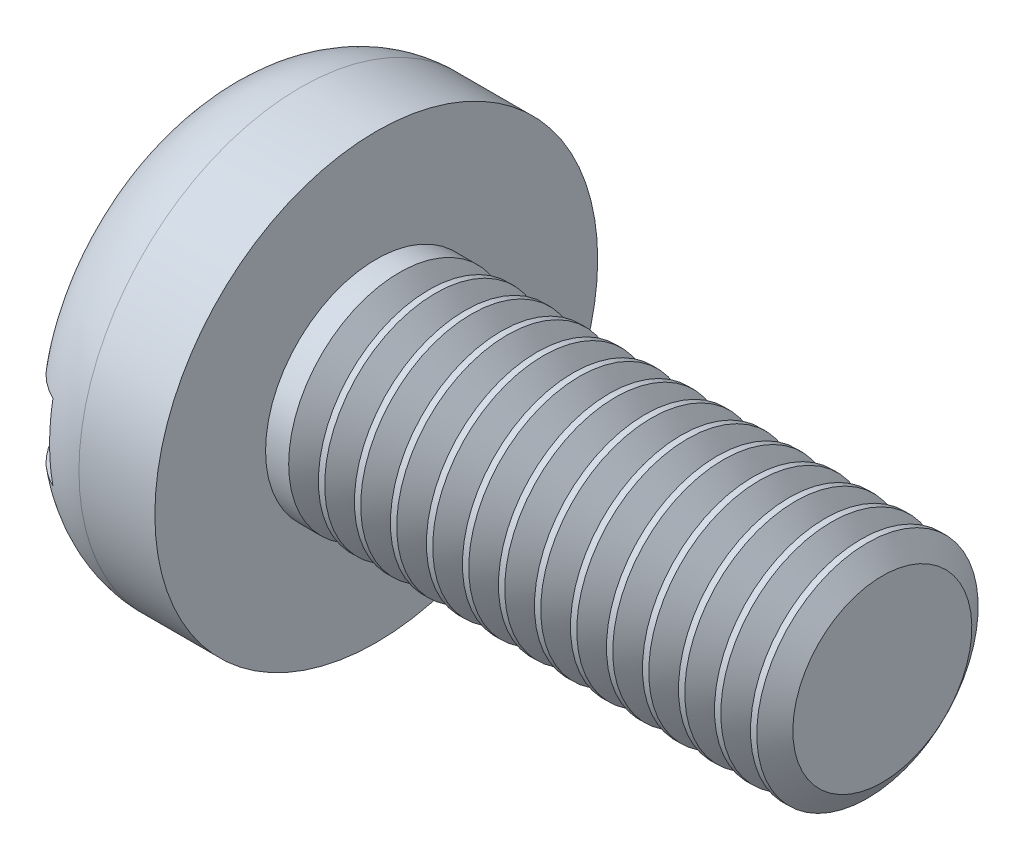
SolidWorks part; units mm, degrees
ref_plane "Plane1" through (0, 0, 0) normal (0, 0, 1) x (1, 0, 0)
ref_plane "Plane2" through (0, 0, 0) normal (0, 1, 0) x (1, 0, 0)
ref_plane "Plane3" through (0, 0, 0) normal (1, 0, 0) x (0, 0, -1)
sketch "BodySke" plane through (0, 0, 0) normal (0, 0, 1) x (1, 0, 0)
  line L0 (2.6, 1.75) -> (2.6, 3.5)
  line L1 (0, 0) -> (0, 2.1)
  line L2 (-25.4, 0) -> (127, 0) construction
  line L3 (10.6, 0) -> (0, 0)
  line L4 (2.6, 1.75) -> (10.6, 1.75)
  line L5 (10.6, 1.75) -> (10.6, 0)
  line L6 (1.4, 3.5) -> (2.6, 3.5)
  line L7 (2.6, -1.75) -> (10.6, -1.75) construction
  line L8 (0, -3.5) -> (2.6, -3.5) construction
  line L9 (3.2, 3.3375) -> (3.2, -6.1875) construction
  line L10 (2.6, 6.35) -> (2.6, -3.175) construction
  arc A0 (0, 2.1) -> (1.4, 3.5) centre (1.4, 2.1) cw
  point P15 (0, 3.5)
  dimension "Head_fillet_rad" = 1.4
  dimension "Diameter" = 3.5
  dimension "Length" = 8
  dimension "Head_ht" = 2.6
  dimension "Head_dia" = 7
  dimension "Advance" = 0.6
  dimension "Thread_nom" = 8
revolve "Base-Revolve" add sketch "BodySke" angle 360 about L2
cosmetic thread "ThreadCosmetic" [suppressed] parameters "Thread_length"=7.4, "Thread_minor"=2.829
sketch "Sketch2" plane through (0, 0, 0) normal (1, 0, 0) x (0, 0, -1)
  line L0 (3.5, -0.6) -> (-3.5, -0.6)
  line L1 (3.5, -0.6) -> (3.5, 0.6)
  line L2 (-3.5, 0.6) -> (3.5, 0.6)
  line L3 (-3.5, 0.6) -> (-3.5, -0.6)
  dimension "D1" = 7
  dimension "Slot_width" = 1.2
  dimension "D2" = 3.5
  dimension "D3" = 0.6
extrude "Slot" cut sketch "Sketch2" along normal blind 0.8
sketch "ThdSchSke" plane through (0, 0, 0) normal (0, 0, 1) x (1, 0, 0)
  line L0 (3.2, -1.4145) -> (2.9651, -1.75)
  line L1 (3.2, -1.4145) -> (3.4349, -1.75)
  line L2 (3.4349, -1.75) -> (3.4349, -2.1875)
  line L3 (-3.175, 0) -> (5.1513, 0) construction
  line L5 (3.4349, -2.1875) -> (2.9651, -2.1875)
  line L6 (2.9651, -2.1875) -> (2.9651, -1.75)
  dimension "Diameter" = 3.5
  dimension "SideAngle" = 55
  dimension "VeeAngle" = 70
  dimension "Thread_minor" = 2.829
  dimension "Overcut" = 4.375
  dimension "Start" = 3.2
revolve "ThreadSchematic" cut sketch "ThdSchSke" angle 360 about L3
pattern_linear "ThdSchPat" count 14 spacing 0.5692 along (1, 0, 0) of "ThreadSchematic"
equation "\"D1@Sketch2\" = \"Head_dia@BodySke\""
equation "\"D2@Sketch2\" = \"D1@Sketch2\" / 2"
equation "\"D3@Sketch2\" = \"Slot_width@Sketch2\" / 2"
equation "\"Thread_length@ThreadCosmetic\" = ((sgn( (\"Length@BodySke\" - \"Advance@BodySke\" ) - \"Thread_nom@BodySke\" )-1)*( (\"Length@BodySke\" - \"Advance@BodySke\" ) - \"Thread_nom@BodySke\" ))/-2+ \"Thread_nom@BodySke\""
equation "\"Thread_minor@ThdSchSke\" = \"Thread_minor@ThreadCosmetic\""
equation "\"Diameter@ThdSchSke\" = \"Diameter@BodySke\""
equation "\"Overcut@ThdSchSke\" = \"Diameter@BodySke\" * 1.25"
equation "\"Start@ThdSchSke\" = \"Head_ht@BodySke\" + \"Length@BodySke\" - \"Thread_length@ThreadCosmetic\"  '---Non-countersunk---"
equation "\"Num_threads@ThdSchPat\" = int( \"Thread_length@ThreadCosmetic\" / \"Advance@BodySke\" + 0.999 )  + 1"
equation "\"Advance@ThdSchPat\" = \"Thread_length@ThreadCosmetic\" /  (\"Num_threads@ThdSchPat\" - 1) 'relax it"
